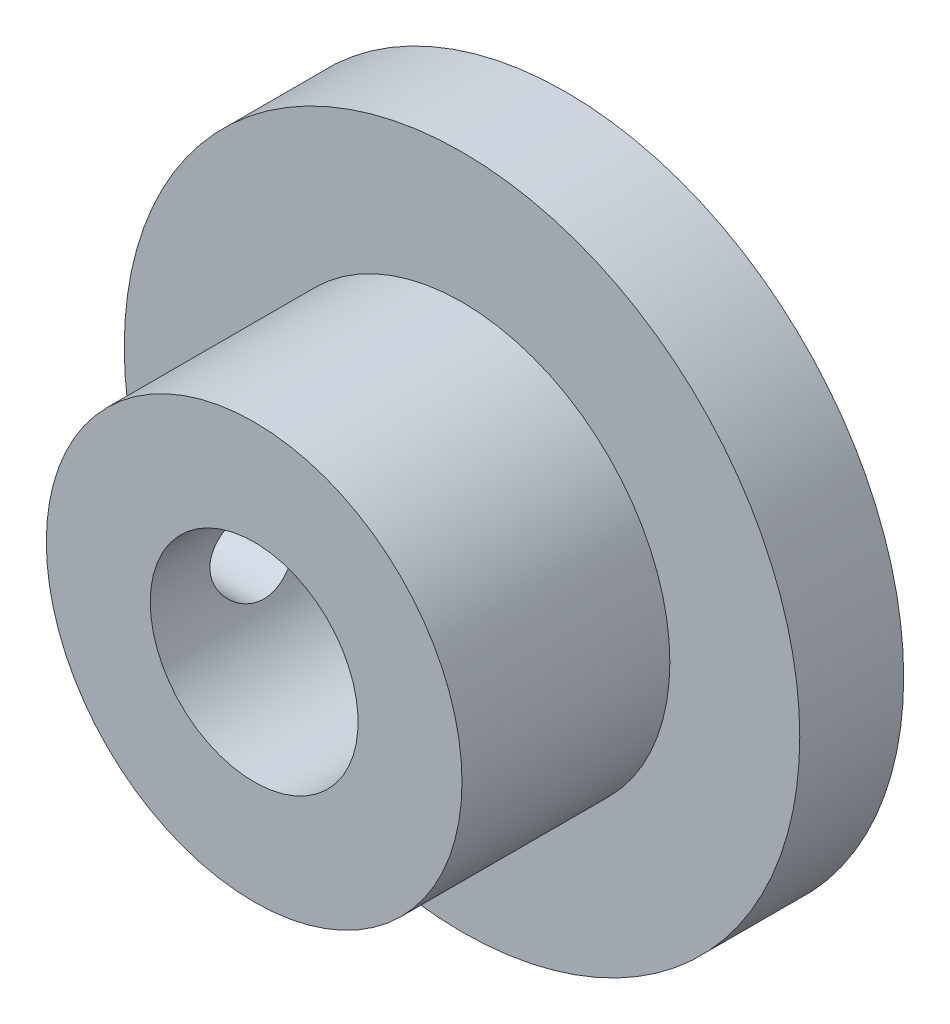
SolidWorks part; units mm, degrees
material "303 Stainless"
ref_plane "Front Plane" through (0, 0, 0) normal (0, 0, 1) x (1, 0, 0)
ref_plane "Top Plane" through (0, 0, 0) normal (0, 1, 0) x (1, 0, 0)
ref_plane "Right Plane" through (0, 0, 0) normal (1, 0, 0) x (0, 0, -1)
sketch "Sketch1" plane through (0, 0, 0) normal (0, 0, 1) x (1, 0, 0)
  circle A0 centre (0, 0) radius 10.3187
  dimension "D1" = 20.6375
extrude "Boss-Extrude1" add sketch "Sketch1" along normal blind 3.175
sketch "Sketch2" plane through (0, 0, 3.175) normal (0, 0, 1) x (1, 0, 0)
  circle A0 centre (0, 0) radius 6.35
  dimension "D1" = 12.7
extrude "Boss-Extrude2" add sketch "Sketch2" along normal blind 6.35
sketch "Sketch3" plane through (0, 0, 0) normal (0, 0, -1) x (-1, 0, 0)
  circle A0 centre (0, 0) radius 3.175
  dimension "D1" = 6.35
extrude "Cut-Extrude1" cut sketch "Sketch3" against normal through all
ref_plane "Plane1" through (-6.35, 0, 0) normal (-1, 0, 0) x (0, 0, 1)
hole_wizard "#6-32 Tapped Hole1" positions "Sketch4" profile "Sketch5" tap size "#6-32" standard "ANSI Inch"
sketch "Sketch4" plane through (-6.35, 0, 0) normal (-1, 0, 0) x (0, 0, 1)
  line L0 (9.525, -6.35) -> (9.525, 6.35) construction
  line L1 (9.525, -6.35) -> (9.525, 6.35) construction
  line L2 (3.175, -10.3187) -> (3.175, 10.3187) construction
  line L3 (3.175, -10.3187) -> (3.175, 10.3187) construction
  line L4 (9.525, 0) -> (3.175, 0) construction
  point P0 (6.35, 0)
sketch "Sketch5" plane through (-6.35, 0, 6.35) normal (0, 1, 0) x (0, 0, 1)
  line L0 (0, 0) -> (0, 3.175)
  line L1 (0, 3.175) -> (1.3525, 3.175)
  line L2 (1.3525, 3.175) -> (1.3525, 0)
  line L5 (1.3525, 0) -> (0, 0)
  line L11 (0, -6.35) -> (0, 107.95) construction
  dimension "Thru Tap Drill Dia." = 2.7051
  dimension "Thru Tap Drill Depth" = 3.175
cosmetic thread "Hole Thread1" parameters "D2"=3.5052
equation "\"hub\"= .5"
equation "\"bore\"= .25"
equation "\"hub l\"= .25"
equation "\"pitch\"= .8125"
equation "\"D1@Sketch1\"=\"pitch\""
equation "\"D1@Sketch2\"=\"hub\""
equation "\"D1@Sketch3\"=\"bore\""
equation "\"face\"= .125"
equation "\"D1@Boss-Extrude1\"=\"face\""
equation "\"D1@Boss-Extrude2\"=\"hub l\""
